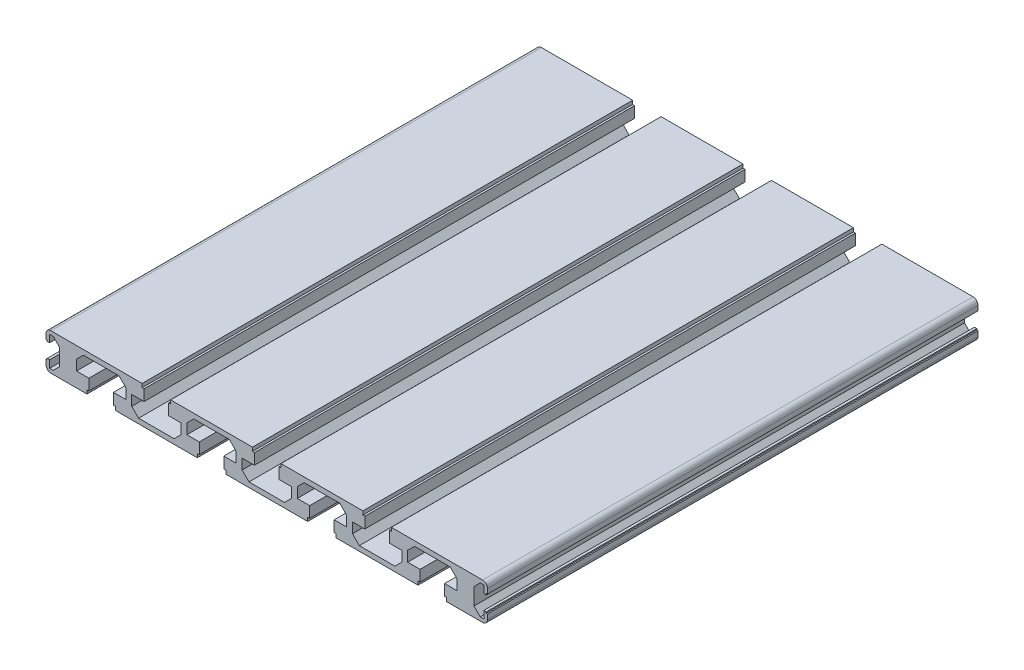
SolidWorks part; units mm, degrees
material "6063-T6"
ref_plane "Спереди" through (0, 0, 0) normal (0, 0, 1) x (1, 0, 0)
ref_plane "Сверху" through (0, 0, 0) normal (0, 1, 0) x (1, 0, 0)
ref_plane "Справа" through (0, 0, 0) normal (1, 0, 0) x (0, 0, -1)
sketch "Эскиз1" plane through (0, 0, 0) normal (0, 0, 1) x (1, 0, 0)
  line L0 (84.1963, 5.3332) -> (84.1963, 2.3332) construction
  line L1 (84.1963, 2.3332) -> (83.1963, 2.3332) construction
  line L2 (83.1963, 2.3332) -> (83.1963, 1.3896) construction
  line L3 (83.1963, -1.7233) -> (83.1963, -2.6668) construction
  line L4 (83.1963, -2.6668) -> (84.1963, -2.6668) construction
  line L5 (84.1963, -2.6668) -> (84.1963, -5.6668) construction
  line L6 (84.1963, -5.6668) -> (80.1963, -5.6668) construction
  line L7 (80.1963, -5.6668) -> (80.1963, -2.6668) construction
  line L8 (80.1963, -2.6668) -> (81.1963, -2.6668) construction
  line L9 (81.1963, -2.6668) -> (81.1963, -1.7233) construction
  line L10 (81.1963, 1.3896) -> (81.1963, 2.3332) construction
  line L11 (81.1963, 2.3332) -> (80.1963, 2.3332) construction
  line L12 (80.1963, 2.3332) -> (80.1963, 5.3332) construction
  line L13 (80.1963, 5.3332) -> (84.1963, 5.3332) construction
  line L14 (-81.8037, -5.6668) -> (-81.8037, -2.6668) construction
  line L15 (-81.8037, -2.6668) -> (-80.8037, -2.6668) construction
  line L16 (-80.8037, -2.6668) -> (-80.8037, -1.7233) construction
  line L17 (-80.8037, 1.3896) -> (-80.8037, 2.3332) construction
  line L18 (-80.8037, 2.3332) -> (-81.8037, 2.3332) construction
  line L19 (-81.8037, 2.3332) -> (-81.8037, 5.3332) construction
  line L20 (-81.8037, 5.3332) -> (-77.8037, 5.3332) construction
  line L21 (-77.8037, 5.3332) -> (-77.8037, 2.3332) construction
  line L22 (-77.8037, 2.3332) -> (-78.8037, 2.3332) construction
  line L23 (-78.8037, 2.3332) -> (-78.8037, 1.3896) construction
  line L24 (-78.8037, -1.7233) -> (-78.8037, -2.6668) construction
  line L25 (-78.8037, -2.6668) -> (-77.8037, -2.6668) construction
  line L26 (-77.8037, -2.6668) -> (-77.8037, -5.6668) construction
  line L27 (-77.8037, -5.6668) -> (-81.8037, -5.6668) construction
  line L28 (-85.8537, -6.1668) -> (-87.3037, -6.1668)
  line L29 (-87.3037, -6.1668) -> (-87.3037, -3.1668)
  line L30 (-87.3037, -3.1668) -> (-88.3037, -3.1668)
  line L31 (-88.3037, -3.1668) -> (-88.3037, -3.6668)
  line L32 (-88.3037, -3.6668) -> (-88.8037, -3.6668)
  line L33 (-88.8037, -3.6668) -> (-88.8037, -5.6668)
  line L34 (-86.8037, -7.6668) -> (-72.1037, -7.6668)
  line L35 (-72.1037, -7.6668) -> (-72.1037, -6.1668)
  line L36 (-72.1037, -6.1668) -> (-71.3037, -6.1668)
  line L37 (-71.3037, -6.1668) -> (-71.3037, -1.6668)
  line L38 (-71.3037, -1.6668) -> (-76.3537, -1.6668)
  line L39 (-76.3537, -1.6668) -> (-76.3537, 2.5332)
  line L40 (-76.3537, 2.5332) -> (-73.5537, 5.3332)
  line L41 (-73.5537, 5.3332) -> (-59.0537, 5.3332)
  line L42 (-59.0537, 5.3332) -> (-56.2537, 2.5332)
  line L43 (-56.2537, 2.5332) -> (-56.2537, -1.6668)
  line L44 (-56.2537, -1.6668) -> (-61.3037, -1.6668)
  line L45 (-61.3037, -1.6668) -> (-61.3037, -6.1668)
  line L46 (-61.3037, -6.1668) -> (-60.5037, -6.1668)
  line L47 (-60.5037, -6.1668) -> (-60.5037, -7.6668)
  line L48 (-60.5037, -7.6668) -> (-27.1037, -7.6668)
  line L49 (-27.1037, -7.6668) -> (-27.1037, -6.1668)
  line L50 (-27.1037, -6.1668) -> (-26.3037, -6.1668)
  line L51 (-26.3037, -6.1668) -> (-26.3037, -1.6668)
  line L52 (-26.3037, -1.6668) -> (-31.3537, -1.6668)
  line L53 (-31.3537, -1.6668) -> (-31.3537, 2.5332)
  line L54 (-31.3537, 2.5332) -> (-28.5537, 5.3332)
  line L55 (-28.5537, 5.3332) -> (-14.0537, 5.3332)
  line L56 (-14.0537, 5.3332) -> (-11.2537, 2.5332)
  line L57 (-11.2537, 2.5332) -> (-11.2537, -1.6668)
  line L58 (-11.2537, -1.6668) -> (-16.3037, -1.6668)
  line L59 (-16.3037, -1.6668) -> (-16.3037, -6.1668)
  line L60 (-16.3037, -6.1668) -> (-15.5037, -6.1668)
  line L61 (-15.5037, -6.1668) -> (-15.5037, -7.6668)
  line L62 (-15.5037, -7.6668) -> (17.8963, -7.6668)
  line L63 (17.8963, -7.6668) -> (17.8963, -6.1668)
  line L64 (17.8963, -6.1668) -> (18.6963, -6.1668)
  line L65 (18.6963, -6.1668) -> (18.6963, -1.6668)
  line L66 (18.6963, -1.6668) -> (13.6463, -1.6668)
  line L67 (13.6463, -1.6668) -> (13.6463, 2.5332)
  line L68 (13.6463, 2.5332) -> (16.4463, 5.3332)
  line L69 (16.4463, 5.3332) -> (30.9463, 5.3332)
  line L70 (30.9463, 5.3332) -> (33.7463, 2.5332)
  line L71 (33.7463, 2.5332) -> (33.7463, -1.6668)
  line L72 (33.7463, -1.6668) -> (28.6963, -1.6668)
  line L73 (28.6963, -1.6668) -> (28.6963, -6.1668)
  line L74 (28.6963, -6.1668) -> (29.4963, -6.1668)
  line L75 (29.4963, -6.1668) -> (29.4963, -7.6668)
  line L76 (29.4963, -7.6668) -> (62.8963, -7.6668)
  line L77 (62.8963, -7.6668) -> (62.8963, -6.1668)
  line L78 (62.8963, -6.1668) -> (63.6963, -6.1668)
  line L79 (63.6963, -6.1668) -> (63.6963, -1.6668)
  line L80 (63.6963, -1.6668) -> (58.6463, -1.6668)
  line L81 (58.6463, -1.6668) -> (58.6463, 2.5332)
  line L82 (58.6463, 2.5332) -> (61.4463, 5.3332)
  line L83 (61.4463, 5.3332) -> (75.9463, 5.3332)
  line L84 (75.9463, 5.3332) -> (78.7463, 2.5332)
  line L85 (78.7463, 2.5332) -> (78.7463, -1.6668)
  line L86 (78.7463, -1.6668) -> (73.6963, -1.6668)
  line L87 (73.6963, -1.6668) -> (73.6963, -6.1668)
  line L88 (73.6963, -6.1668) -> (74.4963, -6.1668)
  line L89 (74.4963, -6.1668) -> (74.4963, -7.6668)
  line L90 (74.4963, -7.6668) -> (89.1963, -7.6668)
  line L91 (91.1963, -5.6668) -> (91.1963, -3.6668)
  line L92 (91.1963, -3.6668) -> (90.6963, -3.6668)
  line L93 (90.6963, -3.6668) -> (90.6963, -3.1668)
  line L94 (90.6963, -3.1668) -> (89.6963, -3.1668)
  line L95 (89.6963, -3.1668) -> (89.6963, -6.1668)
  line L96 (89.6963, -6.1668) -> (88.2463, -6.1668)
  line L97 (88.2463, -6.1668) -> (85.6963, -3.6168)
  line L98 (85.6963, -3.6168) -> (85.6963, 3.2832)
  line L99 (85.6963, 3.2832) -> (88.2463, 5.8332)
  line L100 (88.2463, 5.8332) -> (89.6963, 5.8332)
  line L101 (89.6963, 5.8332) -> (89.6963, 2.8332)
  line L102 (89.6963, 2.8332) -> (90.6963, 2.8332)
  line L103 (90.6963, 2.8332) -> (90.6963, 3.3332)
  line L104 (90.6963, 3.3332) -> (91.1963, 3.3332)
  line L105 (91.1963, 3.3332) -> (91.1963, 5.3332)
  line L106 (89.1963, 7.3332) -> (51.9963, 7.3332)
  line L107 (51.9963, 7.3332) -> (51.9963, 5.8332)
  line L108 (51.9963, 5.8332) -> (51.1963, 5.8332)
  line L109 (51.1963, 5.8332) -> (51.1963, 1.3332)
  line L110 (51.1963, 1.3332) -> (56.2463, 1.3332)
  line L111 (56.2463, 1.3332) -> (56.2463, -2.8668)
  line L112 (56.2463, -2.8668) -> (53.4463, -5.6668)
  line L113 (53.4463, -5.6668) -> (38.9463, -5.6668)
  line L114 (38.9463, -5.6668) -> (36.1463, -2.8668)
  line L115 (36.1463, -2.8668) -> (36.1463, 1.3332)
  line L116 (36.1463, 1.3332) -> (41.1963, 1.3332)
  line L117 (41.1963, 1.3332) -> (41.1963, 5.8332)
  line L118 (41.1963, 5.8332) -> (40.3963, 5.8332)
  line L119 (40.3963, 5.8332) -> (40.3963, 7.3332)
  line L120 (40.3963, 7.3332) -> (6.9963, 7.3332)
  line L121 (6.9963, 7.3332) -> (6.9963, 5.8332)
  line L122 (6.9963, 5.8332) -> (6.1963, 5.8332)
  line L123 (6.1963, 5.8332) -> (6.1963, 1.3332)
  line L124 (6.1963, 1.3332) -> (11.2463, 1.3332)
  line L125 (11.2463, 1.3332) -> (11.2463, -2.8668)
  line L126 (11.2463, -2.8668) -> (8.4463, -5.6668)
  line L127 (8.4463, -5.6668) -> (-6.0537, -5.6668)
  line L128 (-6.0537, -5.6668) -> (-8.8537, -2.8668)
  line L129 (-8.8537, -2.8668) -> (-8.8537, 1.3332)
  line L130 (-8.8537, 1.3332) -> (-3.8037, 1.3332)
  line L131 (-3.8037, 1.3332) -> (-3.8037, 5.8332)
  line L132 (-3.8037, 5.8332) -> (-4.6037, 5.8332)
  line L133 (-4.6037, 5.8332) -> (-4.6037, 7.3332)
  line L134 (-4.6037, 7.3332) -> (-38.0037, 7.3332)
  line L135 (-38.0037, 7.3332) -> (-38.0037, 5.8332)
  line L136 (-38.0037, 5.8332) -> (-38.8037, 5.8332)
  line L137 (-38.8037, 5.8332) -> (-38.8037, 1.3332)
  line L138 (-38.8037, 1.3332) -> (-33.7537, 1.3332)
  line L139 (-33.7537, 1.3332) -> (-33.7537, -2.8668)
  line L140 (-33.7537, -2.8668) -> (-36.5537, -5.6668)
  line L141 (-36.5537, -5.6668) -> (-51.0537, -5.6668)
  line L142 (-51.0537, -5.6668) -> (-53.8537, -2.8668)
  line L143 (-53.8537, -2.8668) -> (-53.8537, 1.3332)
  line L144 (-53.8537, 1.3332) -> (-48.8037, 1.3332)
  line L145 (-48.8037, 1.3332) -> (-48.8037, 5.8332)
  line L146 (-48.8037, 5.8332) -> (-49.6037, 5.8332)
  line L147 (-49.6037, 5.8332) -> (-49.6037, 7.3332)
  line L148 (-49.6037, 7.3332) -> (-86.8037, 7.3332)
  line L149 (-88.8037, 5.3332) -> (-88.8037, 3.3332)
  line L150 (-88.8037, 3.3332) -> (-88.3037, 3.3332)
  line L151 (-88.3037, 3.3332) -> (-88.3037, 2.8332)
  line L152 (-88.3037, 2.8332) -> (-87.3037, 2.8332)
  line L153 (-87.3037, 2.8332) -> (-87.3037, 5.8332)
  line L154 (-87.3037, 5.8332) -> (-85.8537, 5.8332)
  line L155 (-85.8537, 5.8332) -> (-83.3037, 3.2832)
  line L156 (-83.3037, 3.2832) -> (-83.3037, -3.6168)
  line L157 (-83.3037, -3.6168) -> (-85.8537, -6.1668)
  arc A0 (83.1963, 1.3896) -> (83.1963, -1.7233) centre (82.1963, -0.1668) cw construction
  arc A1 (81.1963, -1.7233) -> (81.1963, 1.3896) centre (82.1963, -0.1668) cw construction
  arc A2 (-80.8037, -1.7233) -> (-80.8037, 1.3896) centre (-79.8037, -0.1668) cw construction
  arc A3 (-78.8037, 1.3896) -> (-78.8037, -1.7233) centre (-79.8037, -0.1668) cw construction
  arc A4 (-88.8037, -5.6668) -> (-86.8037, -7.6668) centre (-86.8037, -5.6668) ccw
  arc A5 (89.1963, -7.6668) -> (91.1963, -5.6668) centre (89.1963, -5.6668) ccw
  arc A6 (91.1963, 5.3332) -> (89.1963, 7.3332) centre (89.1963, 5.3332) ccw
  arc A7 (-86.8037, 7.3332) -> (-88.8037, 5.3332) centre (-86.8037, 5.3332) ccw
extrude "Бобышка-Вытянуть1" add sketch "Эскиз1" along normal blind 200
sketch "Эскиз2" plane through (0, 7.3332, 0) normal (0, 1, 0) x (1, 0, 0)
  line L0 (-66.3037, 14.7966) -> (-66.3037, -222.3463) construction
  line L1 (-88.8037, -200) -> (-88.8037, 0) construction
  line L2 (1.1963, 47.8199) -> (1.1963, -244.3449) construction
  line L3 (68.6963, 37.699) -> (68.6963, -217.1007) construction
  line L4 (91.1963, -200) -> (91.1963, 0) construction
  dimension "D1" = 22.5
  dimension "D2" = 90
  dimension "D3" = 22.5
  dimension "D4" = 135
hole_wizard "Зенковка для винта с потайной головкой и внутренним шестигранником M41" positions "Трехмерный эскиз1" profile "Эскиз3" countersink size "M4" standard "ISO"
sketch3d "Трехмерный эскиз1"
  line L0 (-66.3037, 7.3332, -14.7966) -> (-66.3037, 7.3332, 222.3463) construction
  line L1 (-49.6037, 7.3332, 0) -> (-86.8037, 7.3332, 0) construction
  point P0 (-66.3037, 7.3332, 15)
  point P4 (-66.3037, 7.3332, 40)
  point P6 (-66.3037, 7.3332, 65)
  point P8 (-66.3037, 7.3332, 95)
  point P10 (-66.3037, 7.3332, 120)
  point P12 (-66.3037, 7.3332, 145)
  dimension "D1" = 15
  dimension "D2" = 25
  dimension "D3" = 25
  dimension "D4" = 30
  dimension "D5" = 25
  dimension "D6" = 25
sketch "Эскиз3" plane through (-66.3037, 7.3332, 15) normal (1, 0, 0) x (0, 0, 1)
  line L0 (0, 0) -> (0, 26.25)
  line L1 (0, 26.25) -> (2.4, 26.25)
  line L2 (2.4, 26.25) -> (2.4, 2.08)
  line L3 (2.4, 2.08) -> (4.48, 0)
  line L5 (4.48, 0) -> (0, 0)
  line L6 (-2.4, 2.08) -> (-4.48, 0) construction
  line L10 (0, 26.25) -> (-2.4, 26.25) construction
  line L11 (0, -6.35) -> (0, 107.95) construction
  dimension "Диаметр отверстия" = 4.8
  dimension "Глубина отверстия" = 26.25
  dimension "Диаметр передней зенковки" = 8.96
  dimension "Угол передней зенковки" = 90
  dimension "Угол заточки сверла" = 180
pattern_linear "Линейный массив1" [suppressed] count 2 spacing 135
sketch "Эскиз4" plane through (0, 7.3332, 0) normal (0, 1, 0) x (1, 0, 0)
  line L0 (68.6963, 37.699) -> (68.6963, -217.1007) construction
  line L1 (89.1963, -200) -> (51.9963, -200) construction
  circle A0 centre (68.6963, -175) radius 4.1
  dimension "D1" = 8.2
  dimension "D2" = 25
extrude "Вырез-Вытянуть1" [suppressed] cut sketch "Эскиз4" against normal through all
